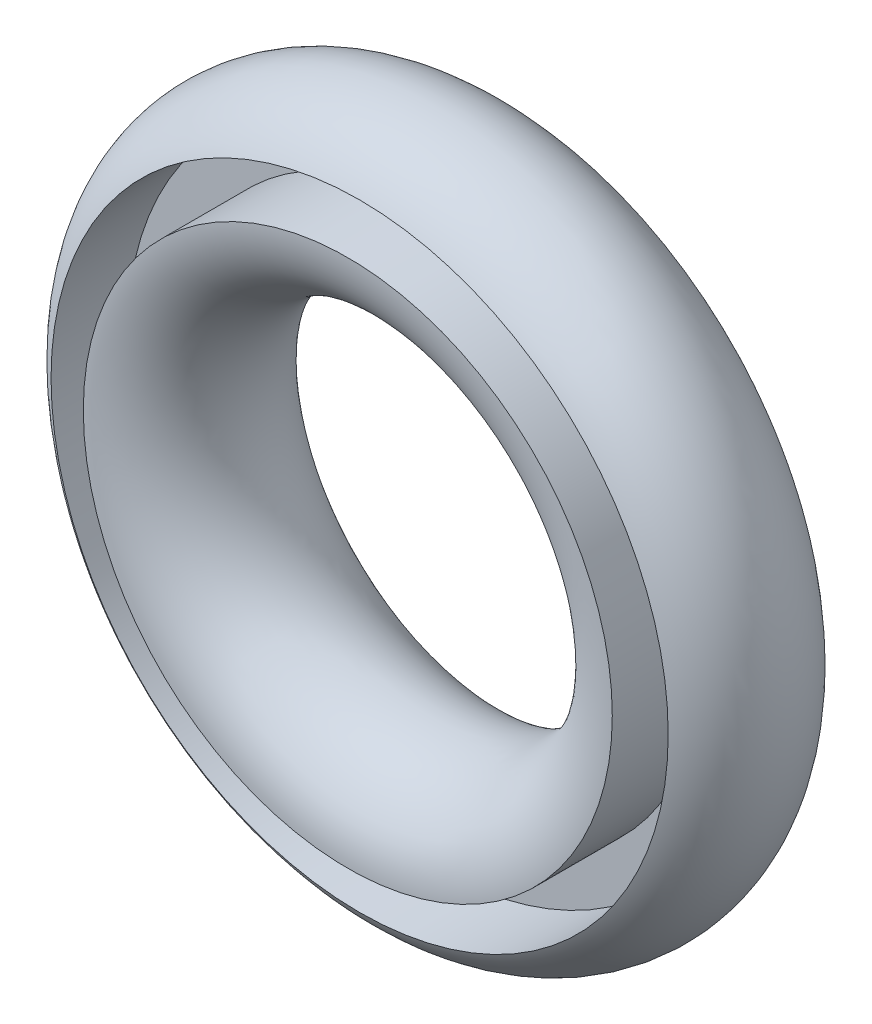
SolidWorks part; units mm, degrees
ref_plane "前视基准面" through (0, 0, 0) normal (0, 0, 1) x (1, 0, 0)
ref_plane "上视基准面" through (0, 0, 0) normal (0, 1, 0) x (1, 0, 0)
ref_plane "右视基准面" through (0, 0, 0) normal (1, 0, 0) x (0, 0, -1)
sketch "草图1" plane through (0, 0, 0) normal (0, 0, 1) x (1, 0, 0)
  circle A0 centre (0, 0) radius 15
  dimension "D1" = 30
sketch "草图2" plane through (0, 0, 0) normal (1, 0, 0) x (0, 0, -1)
  line L0 (0, 15) -> (-5, 15)
  line L1 (0, 15) -> (0, -15) construction
  line L2 (-5, 15) -> (-5, 17.5)
  line L3 (-5, 17.5) -> (0, 17.5)
  line L4 (0, 17.5) -> (0, 15)
  line L5 (9.9232, 0) -> (-16.0724, 0) construction
  line L6 (0, -15) -> (-5, -15)
  line L7 (0, -15) -> (0, -17.5)
  line L8 (0, -17.5) -> (-5, -17.5)
  line L9 (-5, -15) -> (-5, -17.5)
  circle A0 centre (0, -15) radius 5
  dimension "D5" = 10
  dimension "D1" = 5
  dimension "D2" = 2.5
  dimension "D3" = 5
  dimension "D4" = 2.5
revolve "旋转1" add sketch "草图2" angle 360 about L5
